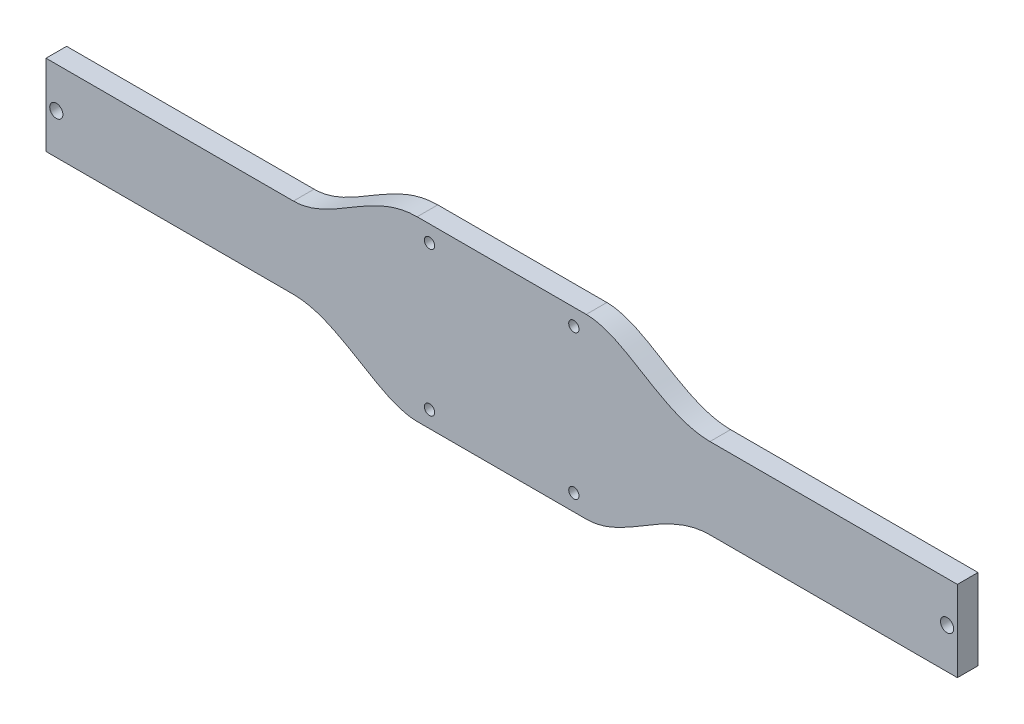
SolidWorks part; units mm, degrees
ref_plane "Front Plane" through (0, 0, 0) normal (0, 0, 1) x (1, 0, 0)
ref_plane "Top Plane" through (0, 0, 0) normal (0, 1, 0) x (1, 0, 0)
ref_plane "Right Plane" through (0, 0, 0) normal (1, 0, 0) x (0, 0, -1)
sketch "Sketch1" plane through (0, 0, 0) normal (0, 0, 1) x (1, 0, 0)
  line L0 (-58.0053, 44.5677) -> (-58.0053, 178.8954) construction
  line L1 (-198.3403, 29.7087) -> (-122.1403, 29.7087)
  line L2 (-198.3403, 29.7087) -> (-198.3403, 4.8167)
  line L3 (-198.3403, 4.8167) -> (-122.1403, 4.8167)
  line L4 (82.3297, 29.7087) -> (82.3297, 4.8167)
  line L5 (-35.7803, 39.4877) -> (-58.0053, 39.4877) construction
  line L6 (-84.0403, 44.5677) -> (-31.9703, 44.5677)
  line L7 (-78.6428, 39.4877) -> (-80.2303, 39.4877) construction
  line L8 (-84.0403, -10.0423) -> (-31.9703, -10.0423)
  line L9 (-31.9703, 44.5677) -> (-31.9703, -10.0423) construction
  line L10 (-121.0196, 17.2627) -> (-198.3403, 17.2627) construction
  line L11 (82.3297, 17.2627) -> (-46.6539, 17.2627) construction
  line L12 (6.1297, 29.7087) -> (82.3297, 29.7087)
  line L13 (6.1297, 4.8167) -> (82.3297, 4.8167)
  line L14 (-80.2303, 39.4877) -> (-80.2303, -4.9623) construction
  line L15 (-80.2303, -4.9623) -> (-35.7803, -4.9623) construction
  line L16 (-35.7803, -4.9623) -> (-35.7803, 39.4877) construction
  line L17 (-58.0053, 39.4877) -> (-58.0053, -4.9623) construction
  line L18 (-35.7803, 17.2627) -> (-58.0053, 17.2627) construction
  line L19 (-39.8806, 44.5677) -> (-59.2794, 44.5677) construction
  line L20 (-15.9436, 29.7087) -> (-39.3232, 29.7087) construction
  line L21 (-39.8806, -10.0423) -> (-59.2794, -10.0423) construction
  line L22 (-153.193, 29.7087) -> (-134.0795, 29.7087) construction
  line L23 (-84.0403, 44.5677) -> (-84.0403, -10.0423) construction
  line L24 (-122.1403, 29.7087) -> (-122.1403, 4.8167) construction
  line L25 (-122.1403, 4.8167) -> (-145.8436, 4.8602) construction
  line L26 (6.1297, 29.7087) -> (6.1297, 4.8167) construction
  circle A0 centre (-80.2303, 39.4877) radius 1.5875
  circle A1 centre (-35.7803, 39.4877) radius 1.5875
  circle A2 centre (-80.2303, -4.9623) radius 1.5875
  circle A3 centre (-35.7803, -4.9623) radius 1.5875
  circle A4 centre (79.1547, 17.2627) radius 2.032
  circle A5 centre (-195.1653, 17.2627) radius 2.032
  spline S0 degree 3 poles (-31.9703, 44.5677) (-19.846, 44.5677) (-8.4825, 29.7087) (6.1297, 29.7087) knots 0 0 0 0 1 1 1 1
  spline S1 degree 3 poles (-31.9703, -10.0423) (-19.846, -10.0423) (-8.1481, 4.8167) (6.1297, 4.8167) knots 0 0 0 0 1 1 1 1
  spline S2 degree 3 poles (-84.0403, -10.0423) (-95.9862, -10.0423) (-107.8207, 4.8167) (-122.1403, 4.8167) knots 0 0 0 0 1 1 1 1
  spline S3 degree 3 poles (-84.0403, 44.5677) (-98.3598, 44.5677) (-110.1943, 29.7087) (-122.1403, 29.7087) knots 0 0 0 0 1 1 1 1
  dimension "D3" = 44.45
  dimension "D9" = 76.2
  dimension "D5" = 3.175
  dimension "D8" = 76.2
  dimension "D13" = 4.064
  dimension "D1" = 24.892
  dimension "D2" = 280.67
  dimension "D4" = 44.45
  dimension "D6" = 114.3
  dimension "D7" = 114.3
  dimension "D10" = 5.08
  dimension "D11" = 5.08
  dimension "D12" = 3.175
extrude "Extrude1" add sketch "Sketch1" along normal blind 6.35
